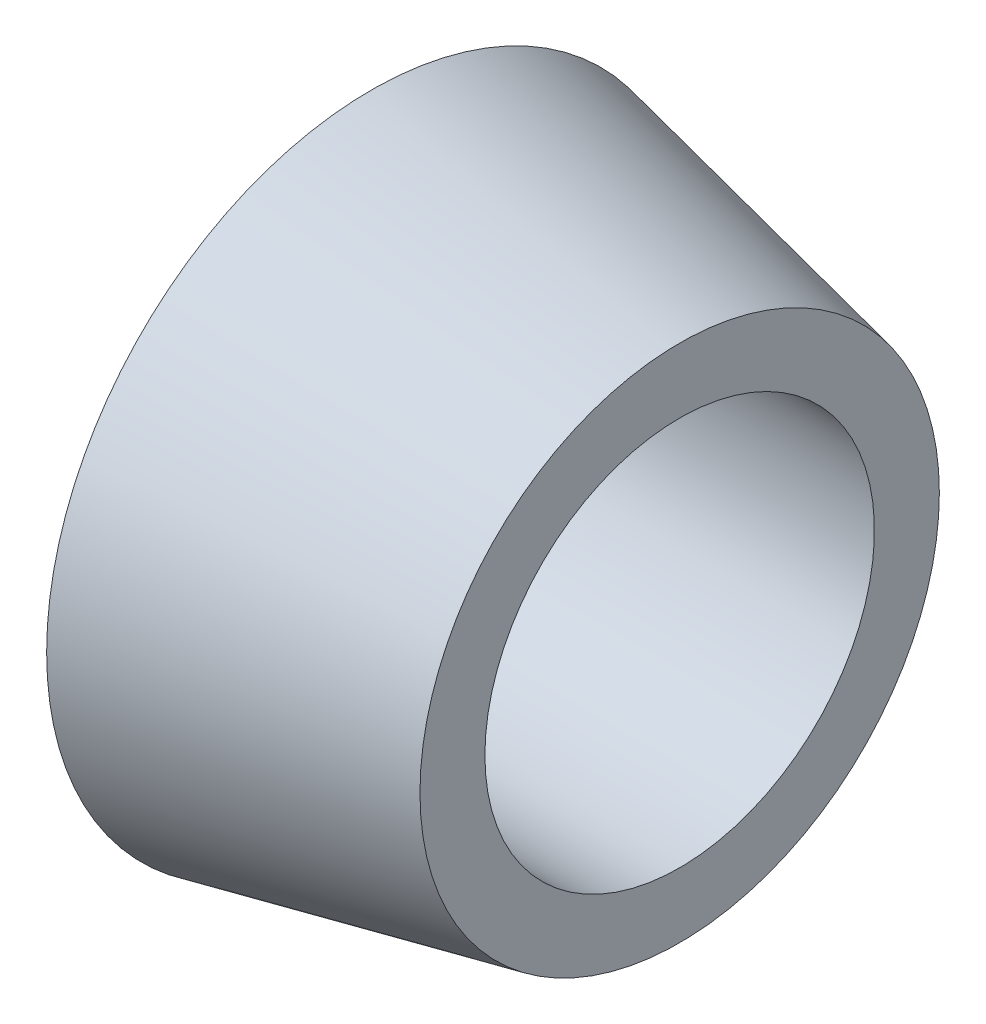
SolidWorks part; units mm, degrees
ref_plane "Płaszczyzna XY" through (0, 0, 0) normal (0, 0, 1) x (1, 0, 0)
ref_plane "Płaszczyzna XZ" through (0, 0, 0) normal (0, 1, 0) x (1, 0, 0)
ref_plane "Płaszczyzna YZ" through (0, 0, 0) normal (1, 0, 0) x (0, 0, -1)
sketch "Szkic1" plane through (0, 0, 0) normal (0, 0, 1) x (1, 0, 0)
  line L0 (0, 6) -> (0, 10)
  line L1 (0, 10) -> (9.5, 8)
  line L2 (9.5, 8) -> (9.5, 6)
  line L3 (9.5, 6) -> (0, 6)
  line L4 (0, 0) -> (22.8523, 0) construction
  dimension "D1" = 12
  dimension "D2" = 8
  dimension "D3" = 9.5
  dimension "D4" = 10
revolve "Obrót1" add sketch "Szkic1" angle 360 about L4
